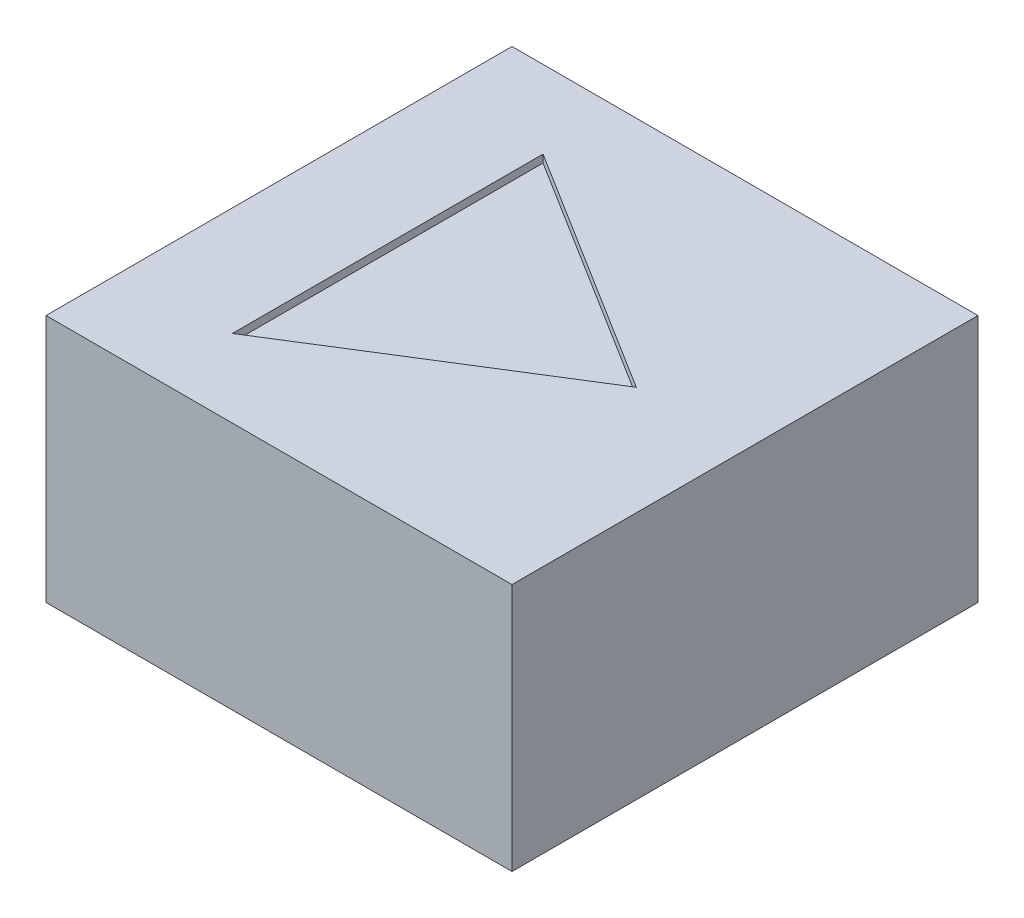
SolidWorks part; units mm, degrees
ref_plane "Front Plane" through (0, 0, 0) normal (0, 0, 1) x (1, 0, 0)
ref_plane "Top Plane" through (0, 0, 0) normal (0, 1, 0) x (1, 0, 0)
ref_plane "Right Plane" through (0, 0, 0) normal (1, 0, 0) x (0, 0, -1)
sketch "Sketch1" plane through (0, 0, 0) normal (0, 1, 0) x (1, 0, 0)
  line L0 (0, -28.5183) -> (0, 36.0562) construction
  line L1 (-46.4836, 0) -> (39.9507, 0) construction
  line L3 (-7.5, 7.5) -> (7.5, 7.5)
  line L4 (-7.5, 7.5) -> (-7.5, -7.5)
  line L5 (-7.5, -7.5) -> (7.5, -7.5)
  line L6 (7.5, 7.5) -> (7.5, -7.5)
  line L7 (-7.5, 7.5) -> (7.5, -7.5) construction
  line L8 (-7.5, -7.5) -> (7.5, 7.5) construction
  point P4 (0, 0)
  dimension "D1" = 15
extrude "Boss-Extrude1" add sketch "Sketch1" along normal blind 8
sketch "Sketch2" plane through (0, 0, 0) normal (0, -1, 0) x (1, 0, 0)
  line L0 (-7.5, 7.5) -> (7.5, -7.5) construction
  line L1 (-7.5, -7.5) -> (7.5, 7.5) construction
  line L2 (-7.5, 0) -> (7.5, 0) construction
  line L3 (-7.5, -7.5) -> (-7.5, 7.5) construction
  line L4 (7.5, 7.5) -> (7.5, -7.5) construction
  circle A0 centre (-3.8891, 3.8891) radius 1
  circle A1 centre (3.8891, -3.8891) radius 1
  circle A2 centre (-3.8891, -3.8891) radius 1
  circle A3 centre (3.8891, 3.8891) radius 1
  dimension "D1" = 11
  dimension "D2" = 2
extrude "Cut-Extrude1" cut sketch "Sketch2" against normal blind 1.5
sketch "Sketch3" plane through (0, 0, 0) normal (0, -1, 0) x (1, 0, 0)
  line L0 (0, 7.5) -> (0, -7.5) construction
  line L1 (-7.5, 7.5) -> (7.5, 7.5) construction
  line L2 (7.5, -7.5) -> (-7.5, -7.5) construction
  line L3 (-7.5, 0) -> (7.5, 0) construction
  line L4 (-7.5, -7.5) -> (-7.5, 7.5) construction
  line L5 (7.5, 7.5) -> (7.5, -7.5) construction
  line L6 (-3.15, 3.15) -> (3.15, 3.15)
  line L7 (-1.75, 1.75) -> (1.75, 1.75)
  line L8 (-1.75, 1.75) -> (-1.75, -1.75)
  line L9 (-1.75, -1.75) -> (1.75, -1.75)
  line L10 (1.75, 1.75) -> (1.75, -1.75)
  line L11 (-1.75, 1.75) -> (1.75, -1.75) construction
  line L12 (-1.75, -1.75) -> (1.75, 1.75) construction
  line L13 (3.15, 3.15) -> (3.15, -3.15)
  line L14 (-3.15, -3.15) -> (3.15, -3.15)
  line L15 (-3.15, 3.15) -> (-3.15, -3.15)
  line L16 (-4.8891, 3.8891) -> (-2.8891, 3.8891) construction
  line L17 (-3.8891, 4.8891) -> (-3.8891, 2.8891) construction
  line L18 (4.2426, -3.5355) -> (-3.5355, 4.2426)
  line L19 (3.8891, -3.8891) -> (-3.8891, -3.8891)
  line L20 (3.8891, -3.8891) -> (3.8891, 3.8891)
  line L21 (3.8891, 3.8891) -> (-3.8891, 3.8891)
  line L22 (-3.8891, -3.8891) -> (-3.8891, 3.8891)
  line L23 (3.8891, -3.8891) -> (-3.8891, 3.8891) construction
  line L24 (3.8891, 3.8891) -> (-3.8891, -3.8891) construction
  line L25 (3.5355, -4.2426) -> (-4.2426, 3.5355)
  line L26 (3.5355, 4.2426) -> (-4.2426, -3.5355)
  line L27 (4.2426, 3.5355) -> (-3.5355, -4.2426)
  circle A0 centre (-3.8891, 3.8891) radius 1 construction
  circle A1 centre (-3.8891, 3.8891) radius 1 construction
  point P12 (0, 0)
  point P31 (0, 0)
  circle M1 centre (3.8891, 3.8891) radius 1
  circle M2 centre (-3.8891, -3.8891) radius 1
  circle M3 centre (3.8891, -3.8891) radius 1
  circle M4 centre (-3.8891, 3.8891) radius 1
  dimension "D1" = 3.5
  dimension "D2" = 1.4
  dimension "D3" = 0.5
  dimension "D4" = 0.5
  dimension "D5" = 0.5
  dimension "D6" = 0.5
extrude "Cut-Extrude2" cut sketch "Sketch3" against normal blind 4 contours L26 L25 L8 | L27 L25 L26 L8 L9 | L25 L27 L9 | L18 L27 L25 L9 L10 | L10 L27 L18 | L27 L10 L7 L26 L18 | L26 L7 L18 | L26 L18 L7 L8 L25 | L27 L18 L26 L25 | L25 L8 L7 L18 L6 L15 | L27 L13 L6 L26 L7 L10 | L25 L14 L13 L18 L10 L9 | L27 L9 L8 L26 L15 L14 | L26 L15 L25 L22 M4 M2 | L27 L13 L18 L20 M1 M3 | L27 L26 L6 L13 M1 | L26 L21 L18 L6 M1 M4 | L27 L14 L15 L26 M2 | L14 L27 L19 L25 M2 M3 | L25 L18 L13 L14 M3 | L25 L15 L6 L18 M4
sketch "Sketch4" plane through (0, 4, 0) normal (0, -1, 0) x (1, 0, 0)
  line L0 (0, 3.8891) -> (0, -3.8891) construction
  line L1 (2.8891, 3.8891) -> (-2.8891, 3.8891) construction
  line L2 (2.8891, -3.8891) -> (-2.8891, -3.8891) construction
  line L3 (-3.8891, 0) -> (3.8891, 0) construction
  line L4 (-3.8891, -2.8891) -> (-3.8891, 2.8891) construction
  line L5 (3.8891, -2.8891) -> (3.8891, 2.8891) construction
  line L7 (2.2, 2.2) -> (-2.2, 2.2)
  line L8 (2.2, 2.2) -> (2.2, -2.2)
  line L9 (2.2, -2.2) -> (-2.2, -2.2)
  line L10 (-2.2, 2.2) -> (-2.2, -2.2)
  line L11 (2.2, 2.2) -> (-2.2, -2.2) construction
  line L12 (2.2, -2.2) -> (-2.2, 2.2) construction
  point P12 (0, 0)
  dimension "D1" = 4.4
extrude "Cut-Extrude3" cut sketch "Sketch4" along normal blind 2.75
sketch "Sketch5" plane through (0, 8, 0) normal (0, 1, 0) x (1, 0, 0)
  line L0 (0, 7.5) -> (0, -7.5) construction
  line L1 (7.5, 7.5) -> (-7.5, 7.5) construction
  line L2 (-7.5, -7.5) -> (7.5, -7.5) construction
  line L3 (-7.5, 0) -> (7.5, 0) construction
  line L4 (-7.5, 7.5) -> (-7.5, -7.5) construction
  line L5 (7.5, -7.5) -> (7.5, 7.5) construction
  line L6 (-4, 7.5) -> (-4, -7.5) construction
  line L7 (4, 7.5) -> (4, -7.5) construction
  line L8 (-7.5, 5) -> (7.5, 5) construction
  line L9 (4, 0) -> (-4, 5)
  line L10 (4, 0) -> (-4, -5)
  line L11 (-4, 5) -> (-4, -5)
  dimension "D1" = 4
  dimension "D2" = 5
extrude "Cut-Extrude4" cut sketch "Sketch5" against normal blind 0.25
fillet "Fillet1" radius 0.75 4 edges at (-1.75, 0, 0) (0, 0, -1.75) (1.75, 0, 0) (0, 0, 1.75)
